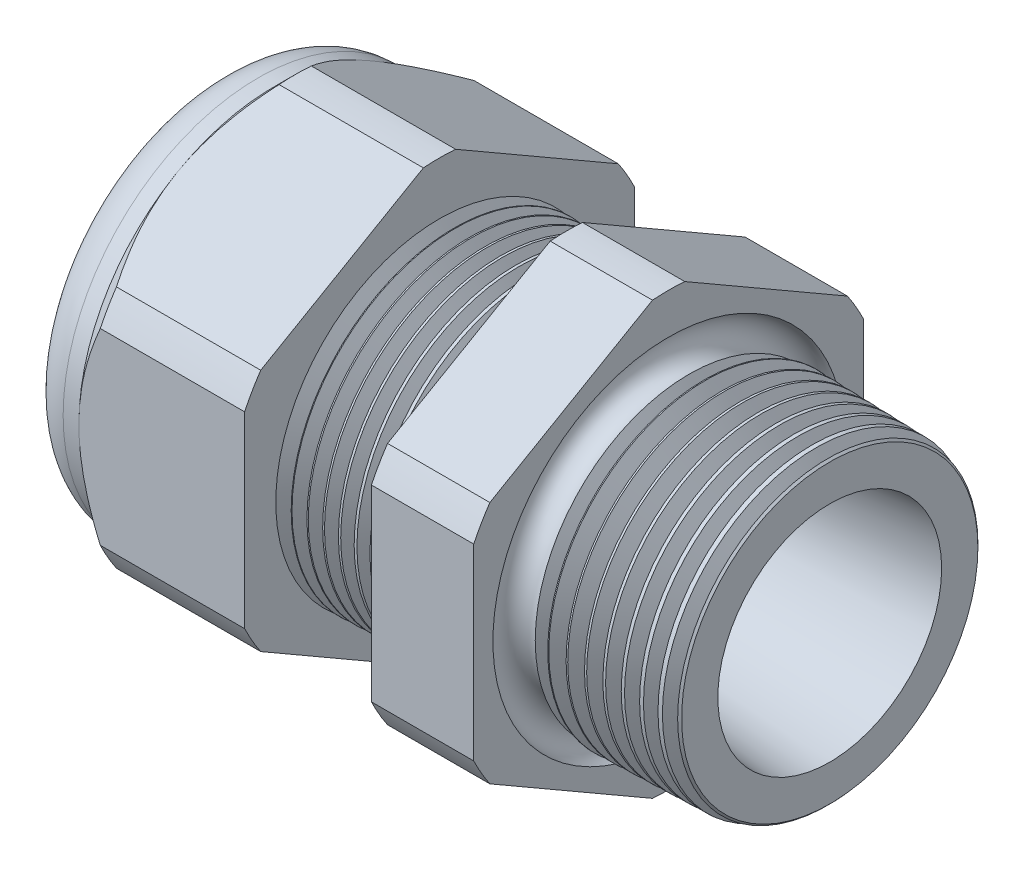
SolidWorks part; units mm, degrees
ref_plane "Front Plane" through (0, 0, 0) normal (0, 0, 1) x (1, 0, 0)
ref_plane "Top Plane" through (0, 0, 0) normal (0, 1, 0) x (1, 0, 0)
ref_plane "Right Plane" through (0, 0, 0) normal (1, 0, 0) x (0, 0, -1)
sketch "Sketch10" plane through (0, 0, 0) normal (0, 0, 1) x (1, 0, 0)
  line L0 (0, 0) -> (-115.3565, 0) construction
  line L1 (-29.972, 3.937) -> (-19.072, 3.937)
  line L2 (0, 5.4696) -> (0, 7.5016)
  line L3 (-7.874, 7.7078) -> (0, 7.5016)
  line L4 (-7.874, 19.05) -> (-7.874, 7.7078)
  line L5 (-7.874, 19.05) -> (-12.874, 19.05)
  line L6 (-12.874, 19.05) -> (-12.874, 7.8387)
  line L7 (-19.072, 8.001) -> (-12.874, 7.8387)
  line L8 (-19.072, 8.001) -> (-19.072, 19.05)
  line L9 (-19.072, 19.05) -> (-27.172, 19.05)
  line L10 (-27.172, 19.05) -> (-27.172, 9.525)
  line L11 (-27.172, 9.525) -> (-29.972, 9.525)
  line L12 (-29.972, 9.525) -> (-29.972, 3.937)
  line L13 (-19.072, 3.937) -> (0, 5.4696)
  dimension "D1" = 29.972
  dimension "D2" = 7.874
  dimension "D3" = 1.5
  dimension "D4" = 2.032
  dimension "A" = 16.002
  dimension "D6" = 19.05
  dimension "D8" = 38.1
  dimension "D9" = 2.8
  dimension "D10" = 8.1
  dimension "D11" = 5
  dimension "D" = 7.874
revolve "Revolve2" add sketch "Sketch10" angle 360 about L0
sketch "Sketch12" plane through (-27.172, 0, 0) normal (-1, 0, 0) x (0, 0, 1)
  line L1 (-0.7885, 10.5433) -> (-8.7365, 5.9545)
  line L2 (-9.525, 4.5888) -> (-9.525, -4.5888)
  line L3 (-8.7365, -5.9545) -> (-0.7885, -10.5433)
  line L4 (0.7885, -10.5433) -> (8.7365, -5.9545)
  line L5 (9.525, -4.5888) -> (9.525, 4.5888)
  line L6 (8.7365, 5.9545) -> (0.7885, 10.5433)
  circle A0 centre (0, 0) radius 9.525 construction
  arc A1 (0.7885, 10.5433) -> (-0.7885, 10.5433) centre (0, 0) ccw
  arc A2 (-8.7365, 5.9545) -> (-9.525, 4.5888) centre (0, 0) ccw
  arc A3 (-9.525, -4.5888) -> (-8.7365, -5.9545) centre (0, 0) ccw
  arc A4 (-0.7885, -10.5433) -> (0.7885, -10.5433) centre (0, 0) ccw
  arc A5 (8.7365, -5.9545) -> (9.525, -4.5888) centre (0, 0) ccw
  arc A6 (9.525, 4.5888) -> (8.7365, 5.9545) centre (0, 0) ccw
  dimension "D2" = 21.1455
  dimension "D1" = 19.05
extrude "Cut-Extrude2" cut sketch "Sketch12" against normal through all flip side to cut
fillet "Fillet4" radius 2.032 1 edges at (-29.972, 0, -9.525)
sketch "Sketch19" plane through (-27.172, 0, 0) normal (-1, 0, 0) x (0, 0, 1)
  line L0 (9.525, 0) -> (9.525, 4.5888) construction
  circle A0 centre (0, 0) radius 9.525
extrude "Cut-Extrude3" cut sketch "Sketch19" against normal blind 2 draft 45 flip side to cut
chamfer "Chamfer1" distance 0.254 angle 45 1 edges at (0, 0, -7.5016)
sketch "Sketch21" plane through (-29.972, 0, 0) normal (-1, 0, 0) x (0, 0, 1)
  circle A0 centre (0, 0) radius 3.937
  circle A2 centre (0, 0) radius 3.937 construction
extrude "plug" add sketch "Sketch21" against normal blind 3.81 separate body
sketch "Sketch22" plane through (-29.972, 0, 0) normal (-1, 0, 0) x (0, 0, 1)
  circle A0 centre (0, 0) radius 3.683
  circle A1 centre (0, 0) radius 3.937 construction
  dimension "D1" = 0.254
extrude "Cut-Extrude4" cut sketch "Sketch22" against normal blind 0.508
sketch "Sketch27" plane through (-29.464, 0, 0) normal (-1, 0, 0) x (0, 0, 1)
  line L0 (-4.3624, 0) -> (4.3624, 0) construction
  circle A0 centre (-2.7904, 0) radius 0.889
  circle A1 centre (0, 0) radius 3.683 construction
  dimension "D1" = 0.0036
  dimension "holedia" = 1.778
extrude "plugholes" cut sketch "Sketch27" against normal through all
pattern_circular "CirPattern1" count 2 over 360 about axis through (0, 0, 0) along (1, 0, 0) of "plugholes"
sketch "Sketch28" [suppressed] plane through (-29.464, 0, 0) normal (-1, 0, 0) x (0, 0, 1)
  circle A0 centre (0, 0) radius 0.762
  dimension "midholedia" = 1.778
extrude "midhole" [suppressed] cut sketch "Sketch28" against normal through all
sketch "Sketch29" plane through (0, 0, 0) normal (0, 0, 1) x (1, 0, 0)
  line L0 (-19.072, 8.001) -> (-18.339, 7.9818)
  line L1 (-12.874, 7.8387) -> (-19.072, 8.001) construction
  line L2 (-18.339, 7.9818) -> (-18.7221, 7.3566)
  line L3 (-18.7221, 7.3566) -> (-19.072, 8.001)
  dimension "D1" = 60
  dimension "D2" = 60
  dimension "D3" = 0.635
revolve "Cut-Revolve1" cut sketch "Sketch29" angle 360 about axis through (0, 0, 0) along (-1, 0, 0)
pattern_linear "LPattern1" count 8 spacing 0.762 along (1, 0, 0) of "Cut-Revolve1"
sketch "Sketch30" plane through (0, 0, 0) normal (0, 0, 1) x (1, 0, 0)
  line L0 (-7.874, 7.7078) -> (-6.9944, 7.6847)
  line L1 (-7.874, 10.5433) -> (-7.874, 5.9545) construction
  line L2 (-0.2539, 7.5082) -> (-7.874, 7.7078) construction
  line L3 (-6.9944, 7.6847) -> (-7.4542, 6.9345)
  line L4 (-7.4542, 6.9345) -> (-7.874, 7.7078)
  dimension "D1" = 60
  dimension "D2" = 60
  dimension "D3" = 0.762
revolve "Cut-Revolve2" cut sketch "Sketch30" angle 360 about axis through (0, 0, 0) along (-1, 0, 0)
pattern_linear "LPattern2" count 9 spacing 0.889 along (1, 0, 0) of "Cut-Revolve2"
sketch "Sketch31" [suppressed] plane through (-38.354, 0, 0) normal (-1, 0, 0) x (0, 0, 1)
  line L0 (-1.905, 1.905) -> (1.905, 1.905)
  line L1 (-1.905, -1.905) -> (1.905, -1.905)
  circle A0 centre (0, 0) radius 1.905 construction
  arc A1 (-1.905, 1.905) -> (-1.905, -1.905) centre (-1.905, 0) ccw
  arc A2 (1.905, 1.905) -> (1.905, -1.905) centre (1.905, 0) cw
extrude "Cut-Extrude5" [suppressed] cut sketch "Sketch31" against normal through all
sketch "Sketch32" plane through (0, 0, 0) normal (0, 0, 1) x (1, 0, 0)
  line L0 (-7.874, 10.5433) -> (-7.874, 5.9545) construction
  circle A0 centre (-7.747, 7.7078) radius 0.889
  dimension "D2" = 1.778
  dimension "D1" = 0.127
revolve "Cut-Revolve3" cut sketch "Sketch32" angle 360 about axis through (0, 0, 0) along (-1, 0, 0)
